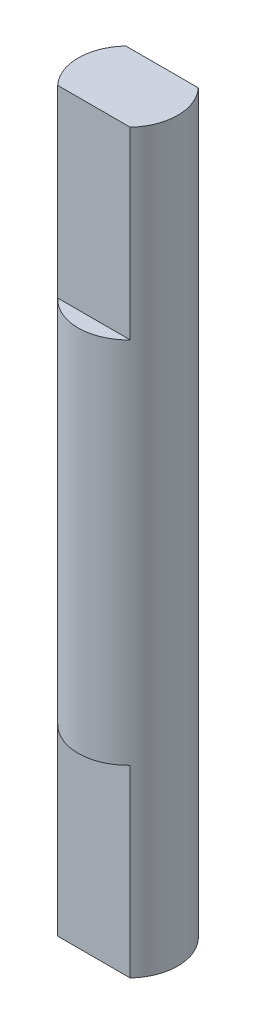
SolidWorks part; units mm, degrees
ref_plane "Alzado" through (0, 0, 0) normal (0, 0, 1) x (1, 0, 0)
ref_plane "Planta" through (0, 0, 0) normal (0, 1, 0) x (1, 0, 0)
ref_plane "Vista lateral" through (0, 0, 0) normal (1, 0, 0) x (0, 0, -1)
sketch "Croquis1" plane through (0, 0, 0) normal (0, 1, 0) x (1, 0, 0)
  circle A0 centre (0, 0) radius 2.7
  dimension "D1" = 5.4
extrude "Saliente-Extruir1" add sketch "Croquis1" along normal mid plane 20
sketch "Croquis2" plane through (0, 10, 0) normal (0, 1, 0) x (1, 0, 0)
  line L0 (1.9666, 1.85) -> (-1.9666, 1.85)
  line L2 (1.9666, -1.85) -> (-1.9666, -1.85)
  arc A0 (1.9666, -1.85) -> (1.9666, 1.85) centre (0, 0) ccw
  circle A1 centre (0, 0) radius 2.7
  arc A2 (-1.9666, 1.85) -> (-1.9666, -1.85) centre (0, 0) ccw
  dimension "D2" = 1.85
  dimension "D3" = 1.85
  dimension "D1" = 0
extrude "Saliente-Extruir2" add sketch "Croquis2" along normal blind 10
mirror "Simetría1" about plane through (0, 0, 0) normal (0, 1, 0) of "Saliente-Extruir2"
